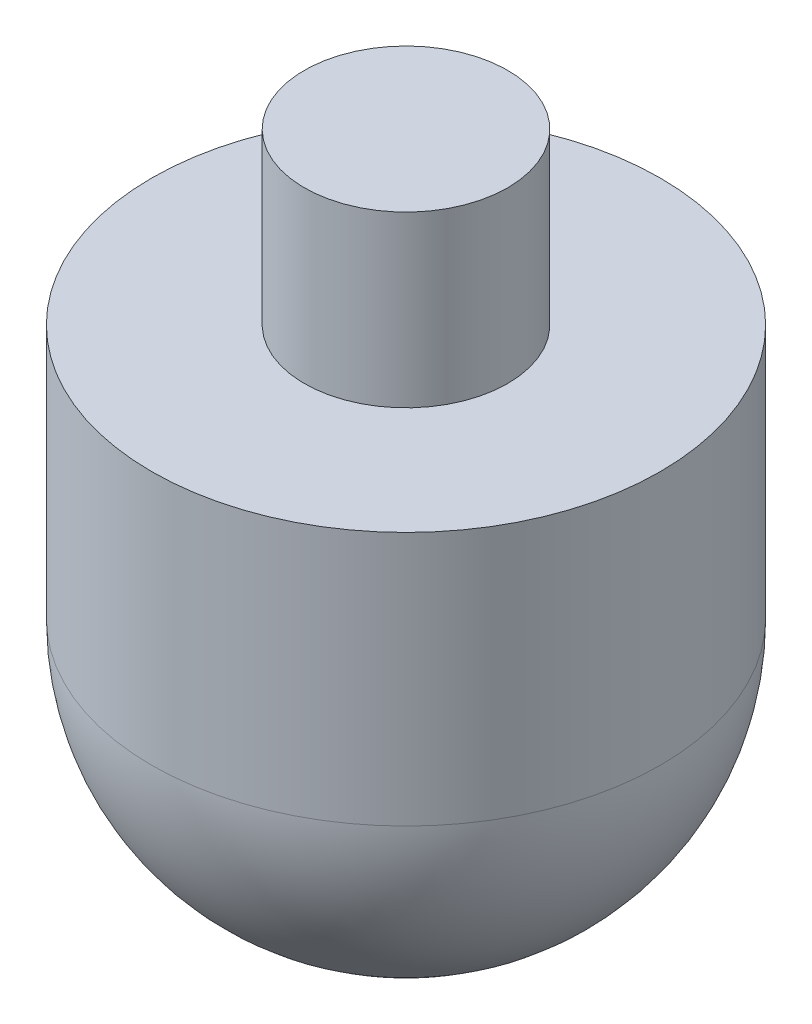
SolidWorks part; units mm, degrees
ref_plane "Front Plane" through (0, 0, 0) normal (0, 0, 1) x (1, 0, 0)
ref_plane "Top Plane" through (0, 0, 0) normal (0, 1, 0) x (1, 0, 0)
ref_plane "Right Plane" through (0, 0, 0) normal (1, 0, 0) x (0, 0, -1)
sketch "Sketch1" plane through (0, 0, 0) normal (0, 0, 1) x (1, 0, 0)
  line L0 (0, 0) -> (0, -40) construction
  line L1 (0, 0) -> (6, 0)
  line L2 (6, 0) -> (6, -10)
  line L3 (6, -10) -> (15, -10)
  line L4 (15, -10) -> (15, -40)
  line L5 (15, -40) -> (0, -40)
  line L6 (0, -40) -> (0, 0)
  line L7 (0, 0) -> (0, 6.8878) construction
  dimension "D1" = 12
  dimension "D2" = 30
  dimension "D3" = 40
  dimension "D4" = 10
revolve "Revolve2" add sketch "Sketch1" angle 360 about L6
fillet "Fillet7" radius 15 1 edges at (15, -40, 0)
